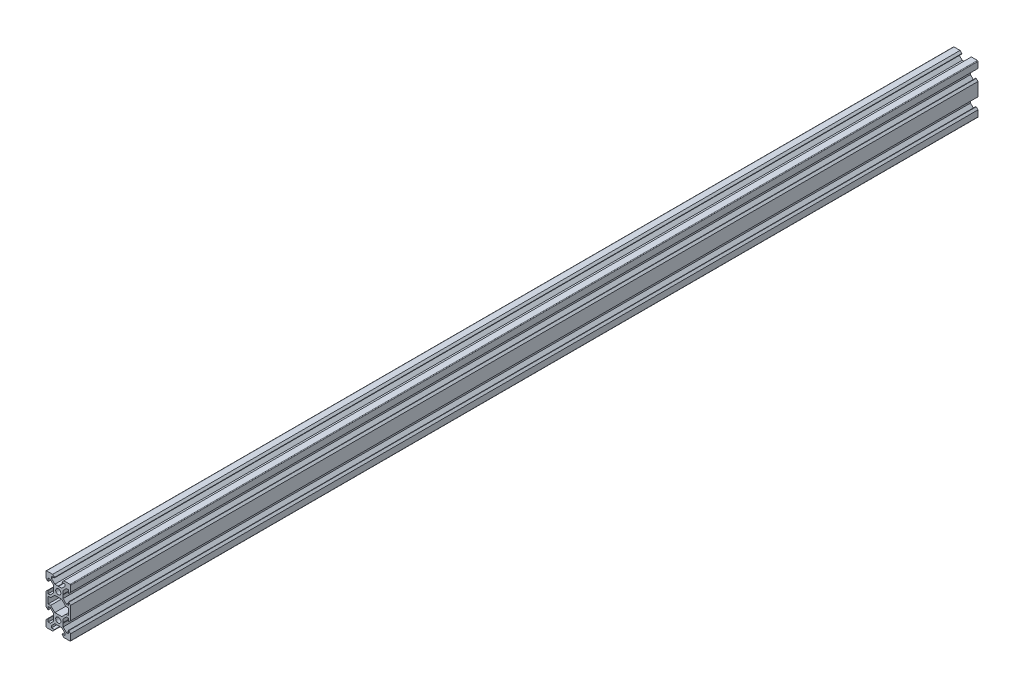
SolidWorks part; units mm, degrees
material "6061-T6 (SS)"
ref_plane "Front Plane" through (0, 0, 0) normal (0, 0, 1) x (1, 0, 0)
ref_plane "Top Plane" through (0, 0, 0) normal (0, 1, 0) x (1, 0, 0)
ref_plane "Right Plane" through (0, 0, 0) normal (1, 0, 0) x (0, 0, -1)
sketch "Sketch1" plane through (0, 0, 0) normal (0, 0, 1) x (1, 0, 0)
  line L0 (0, 0) -> (10, 0) construction
  line L1 (9.5, -20) -> (-9.5, -20)
  line L2 (10, -19.5) -> (10, 19.5)
  line L3 (9.5, 20) -> (-9.5, 20)
  line L4 (-10, -19.5) -> (-10, 19.5)
  line L5 (10, -20) -> (-10, 20) construction
  line L6 (10, 20) -> (-10, -20) construction
  line L7 (-8.2, -2.7) -> (-8.2, 2.7)
  line L8 (-8.2, 2.7) -> (-6.2393, 2.7)
  line L9 (-6.2393, 2.7) -> (-2.8393, 6.1)
  line L10 (-2.8393, 6.1) -> (2.8393, 6.1)
  line L11 (0, 6.1) -> (0, 0) construction
  line L12 (0, 0) -> (-8.2, 0) construction
  line L13 (6.2393, 2.7) -> (2.8393, 6.1)
  line L14 (8.2, 2.7) -> (6.2393, 2.7)
  line L15 (8.2, -2.7) -> (8.2, 2.7)
  line L16 (8.2, -2.7) -> (6.2393, -2.7)
  line L17 (6.2393, -2.7) -> (2.8393, -6.1)
  line L18 (-2.8393, -6.1) -> (2.8393, -6.1)
  line L19 (-6.2393, -2.7) -> (-2.8393, -6.1)
  line L20 (-8.2, -2.7) -> (-6.2393, -2.7)
  line L21 (0, 6.1) -> (0, 10) construction
  line L22 (0, 10) -> (-5.0927, 4.9073) construction
  line L23 (0, 10) -> (10, 10) construction
  line L24 (3.69, 10) -> (3.9, 10.21)
  line L25 (3.9, 10.21) -> (3.9, 12.8393)
  line L26 (3.9, 12.8393) -> (6.5607, 15.5)
  line L27 (6.5607, 15.5) -> (8.2, 15.5)
  line L28 (8.2, 15.5) -> (8.2, 13.125)
  line L29 (8.2, 13.125) -> (8.545, 13.125)
  line L30 (8.545, 13.125) -> (10, 14.58)
  line L31 (10, 14.58) -> (10, 5.42)
  line L32 (0, 10) -> (5.9132, 15.9132) construction
  line L33 (8.545, 6.875) -> (10, 5.42)
  line L34 (8.2, 6.875) -> (8.545, 6.875)
  line L35 (8.2, 4.5) -> (8.2, 6.875)
  line L36 (6.5607, 4.5) -> (8.2, 4.5)
  line L37 (3.9, 7.1607) -> (6.5607, 4.5)
  line L38 (3.9, 9.79) -> (3.9, 7.1607)
  line L39 (3.69, 10) -> (3.9, 9.79)
  line L40 (0, -10) -> (10, -10) construction
  line L41 (3.69, -10) -> (3.9, -9.79)
  line L42 (3.9, -9.79) -> (3.9, -7.1607)
  line L43 (3.9, -7.1607) -> (6.5607, -4.5)
  line L44 (6.5607, -4.5) -> (8.2, -4.5)
  line L45 (8.2, -4.5) -> (8.2, -6.875)
  line L46 (8.2, -6.875) -> (8.545, -6.875)
  line L47 (8.545, -6.875) -> (10, -5.42)
  line L48 (10, -5.42) -> (10, -14.58)
  line L49 (0, -10) -> (5.9132, -4.0868) construction
  line L50 (8.545, -13.125) -> (10, -14.58)
  line L51 (8.2, -13.125) -> (8.545, -13.125)
  line L52 (8.2, -15.5) -> (8.2, -13.125)
  line L53 (6.5607, -15.5) -> (8.2, -15.5)
  line L54 (3.9, -12.8393) -> (6.5607, -15.5)
  line L55 (3.9, -10.21) -> (3.9, -12.8393)
  line L56 (3.69, -10) -> (3.9, -10.21)
  line L57 (0, 10) -> (0, 20) construction
  line L58 (0, 13.69) -> (-0.21, 13.9)
  line L59 (-0.21, 13.9) -> (-2.8393, 13.9)
  line L60 (-2.8393, 13.9) -> (-5.5, 16.5607)
  line L61 (-5.5, 16.5607) -> (-5.5, 18.2)
  line L62 (-5.5, 18.2) -> (-3.125, 18.2)
  line L63 (-3.125, 18.2) -> (-3.125, 18.545)
  line L64 (-3.125, 18.545) -> (-4.58, 20)
  line L65 (-4.58, 20) -> (4.58, 20)
  line L66 (0, 10) -> (-5.9132, 15.9132) construction
  line L67 (3.125, 18.545) -> (4.58, 20)
  line L68 (3.125, 18.2) -> (3.125, 18.545)
  line L69 (5.5, 18.2) -> (3.125, 18.2)
  line L70 (5.5, 16.5607) -> (5.5, 18.2)
  line L71 (2.8393, 13.9) -> (5.5, 16.5607)
  line L72 (0.21, 13.9) -> (2.8393, 13.9)
  line L73 (0, 13.69) -> (0.21, 13.9)
  line L74 (0, 10) -> (-10, 10) construction
  line L75 (-3.69, 10) -> (-3.9, 9.79)
  line L76 (-3.9, 9.79) -> (-3.9, 7.1607)
  line L77 (-3.9, 7.1607) -> (-6.5607, 4.5)
  line L78 (-6.5607, 4.5) -> (-8.2, 4.5)
  line L79 (-8.2, 4.5) -> (-8.2, 6.875)
  line L80 (-8.2, 6.875) -> (-8.545, 6.875)
  line L81 (-8.545, 6.875) -> (-10, 5.42)
  line L82 (-10, 5.42) -> (-10, 14.58)
  line L83 (0, 10) -> (-5.9132, 4.0868) construction
  line L84 (-8.545, 13.125) -> (-10, 14.58)
  line L85 (-8.2, 13.125) -> (-8.545, 13.125)
  line L86 (-8.2, 15.5) -> (-8.2, 13.125)
  line L87 (-6.5607, 15.5) -> (-8.2, 15.5)
  line L88 (-3.9, 12.8393) -> (-6.5607, 15.5)
  line L89 (-3.9, 10.21) -> (-3.9, 12.8393)
  line L90 (-3.69, 10) -> (-3.9, 10.21)
  line L91 (0, -10) -> (-10, -10) construction
  line L92 (-3.69, -10) -> (-3.9, -10.21)
  line L93 (-3.9, -10.21) -> (-3.9, -12.8393)
  line L94 (-3.9, -12.8393) -> (-6.5607, -15.5)
  line L95 (-6.5607, -15.5) -> (-8.2, -15.5)
  line L96 (-8.2, -15.5) -> (-8.2, -13.125)
  line L97 (-8.2, -13.125) -> (-8.545, -13.125)
  line L98 (-8.545, -13.125) -> (-10, -14.58)
  line L99 (-10, -14.58) -> (-10, -5.42)
  line L100 (0, -10) -> (-5.9132, -15.9132) construction
  line L101 (-8.545, -6.875) -> (-10, -5.42)
  line L102 (-8.2, -6.875) -> (-8.545, -6.875)
  line L103 (-8.2, -4.5) -> (-8.2, -6.875)
  line L104 (-6.5607, -4.5) -> (-8.2, -4.5)
  line L105 (-3.9, -7.1607) -> (-6.5607, -4.5)
  line L106 (-3.9, -9.79) -> (-3.9, -7.1607)
  line L107 (-3.69, -10) -> (-3.9, -9.79)
  line L108 (0, -10) -> (0, -20) construction
  line L109 (0, -13.69) -> (0.21, -13.9)
  line L110 (0.21, -13.9) -> (2.8393, -13.9)
  line L111 (2.8393, -13.9) -> (5.5, -16.5607)
  line L112 (5.5, -16.5607) -> (5.5, -18.2)
  line L113 (5.5, -18.2) -> (3.125, -18.2)
  line L114 (3.125, -18.2) -> (3.125, -18.545)
  line L115 (3.125, -18.545) -> (4.58, -20)
  line L116 (4.58, -20) -> (-4.58, -20)
  line L117 (0, -10) -> (5.9132, -15.9132) construction
  line L118 (-3.125, -18.545) -> (-4.58, -20)
  line L119 (-3.125, -18.2) -> (-3.125, -18.545)
  line L120 (-5.5, -18.2) -> (-3.125, -18.2)
  line L121 (-5.5, -16.5607) -> (-5.5, -18.2)
  line L122 (-2.8393, -13.9) -> (-5.5, -16.5607)
  line L123 (-0.21, -13.9) -> (-2.8393, -13.9)
  line L124 (0, -13.69) -> (-0.21, -13.9)
  circle A0 centre (0, 10) radius 2.1
  circle A1 centre (0, -10) radius 2.1
  arc A2 (-9.5, -20) -> (-10, -19.5) centre (-9.5, -19.5) cw
  arc A3 (9.5, -20) -> (10, -19.5) centre (9.5, -19.5) ccw
  arc A4 (10, 19.5) -> (9.5, 20) centre (9.5, 19.5) ccw
  arc A5 (-9.5, 20) -> (-10, 19.5) centre (-9.5, 19.5) ccw
  point P0 (0, 0)
  point P35 (8.2, 0)
  dimension "D4" = 4.2
  dimension "D5" = 0.5
  dimension "D1" = 20
  dimension "D2" = 40
  dimension "D3" = 20
  dimension "D6" = 5.4
  dimension "D7" = 12.2
  dimension "D8" = 8.2
  dimension "D9" = 45
  dimension "D10" = 10
  dimension "D11" = 1.5
  dimension "D12" = 10
  dimension "D13" = 11
  dimension "D14" = 4.3
  dimension "D15" = 1.8
  dimension "D16" = 0.21
  dimension "D17" = 45
  dimension "D18" = 9.16
  dimension "D19" = 1.5
  dimension "D20" = 6.25
  dimension "D21" = 10
  dimension "D22" = 11
  dimension "D23" = 4.3
  dimension "D24" = 1.8
  dimension "D25" = 0.21
  dimension "D26" = 45
  dimension "D27" = 9.16
  dimension "D28" = 1.5
  dimension "D29" = 6.25
  dimension "D30" = 10
  dimension "D31" = 11
  dimension "D32" = 4.3
  dimension "D33" = 1.8
  dimension "D34" = 0.21
  dimension "D35" = 45
  dimension "D36" = 9.16
  dimension "D37" = 1.5
  dimension "D38" = 6.25
  dimension "D39" = 10
  dimension "D40" = 11
  dimension "D41" = 4.3
  dimension "D42" = 1.8
  dimension "D43" = 0.21
  dimension "D44" = 45
  dimension "D45" = 9.16
  dimension "D46" = 1.5
  dimension "D47" = 6.25
  dimension "D48" = 10
  dimension "D49" = 11
  dimension "D50" = 4.3
  dimension "D51" = 1.8
  dimension "D52" = 0.21
  dimension "D53" = 45
  dimension "D54" = 9.16
  dimension "D55" = 1.5
  dimension "D56" = 6.25
  dimension "D57" = 10
  dimension "D58" = 11
  dimension "D59" = 4.3
  dimension "D60" = 1.8
  dimension "D61" = 0.21
  dimension "D62" = 45
  dimension "D63" = 9.16
  dimension "D64" = 1.5
  dimension "D65" = 6.25
extrude "Boss-Extrude1" add sketch "Sketch1" along normal blind 738 contours L39 L24 L25 L26 L27 L28 L29 L30 L2 A4 L3 L67 L68 L69 L70 L71 L72 L73 L58 L59 L60 L61 L62 L63 L64 A5 L4 L84 L85 L86 L87 L88 L89 L90 L75 L76 L77 L78 L79 L80 L81 L101 L102 L103 L104 L105 L106 L107 L92
